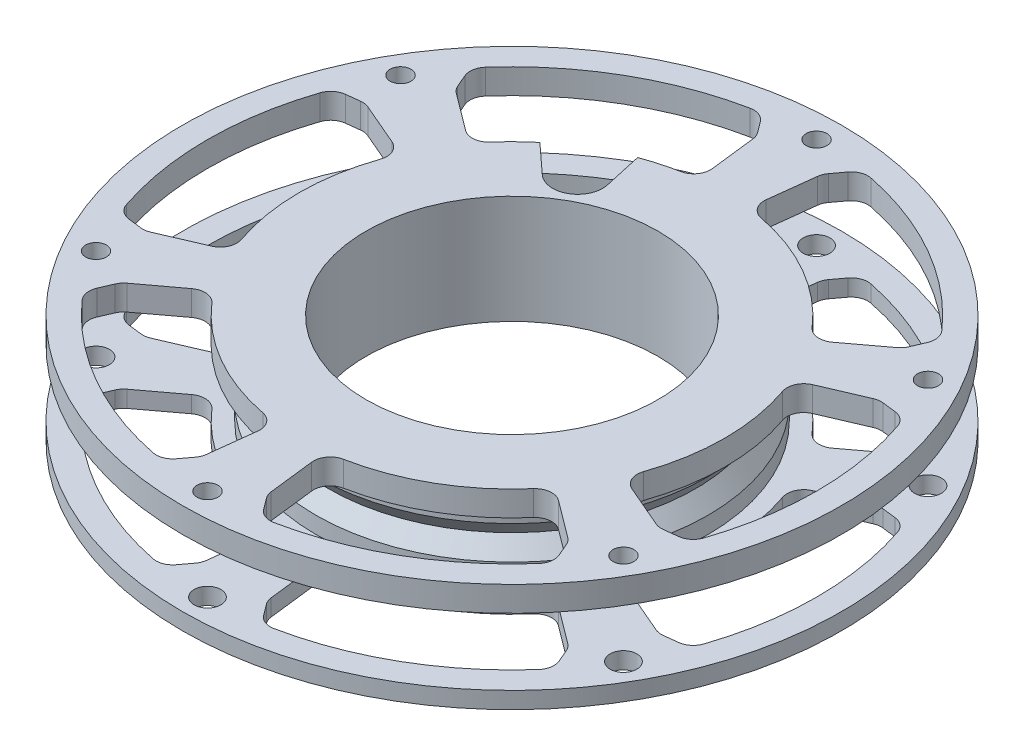
SolidWorks part; units mm, degrees
material "6061 Alloy"
ref_plane "Front Plane" through (0, 0, 0) normal (0, 0, 1) x (1, 0, 0)
ref_plane "Top Plane" through (0, 0, 0) normal (0, 1, 0) x (1, 0, 0)
ref_plane "Right Plane" through (0, 0, 0) normal (1, 0, 0) x (0, 0, -1)
sketch "Sketch1" plane through (0, 0, 0) normal (0, 1, 0) x (1, 0, 0)
  line L0 (0, 0) -> (0, 36.5) construction
  line L1 (0, 0) -> (31.6099, 18.25) construction
  line L2 (0, 0) -> (31.6099, -18.25) construction
  line L3 (0, 0) -> (0, -36.5) construction
  line L4 (0, 0) -> (-31.6099, -18.25) construction
  line L5 (0, 0) -> (-31.6099, 18.25) construction
  point P0 (0, 0)
  point P1 (0, 36.5)
  point P7 (31.6099, 18.25)
  point P9 (31.6099, -18.25)
  point P11 (0, -36.5)
  point P13 (-31.6099, -18.25)
  point P15 (-31.6099, 18.25)
  point P17 (0, 0)
  dimension "D1" = 36.5
  dimension "D2" = 6
sketch "Sketch2" plane through (0, 0, 0) normal (0, 1, 0) x (1, 0, 0)
  line L0 (0, 39.5) -> (12.1614, 39.5) construction
  circle A0 centre (0, 0) radius 39.5
  dimension "D1" = 3
extrude "Boss-Extrude1" add sketch "Sketch2" along normal blind 2
sketch "Sketch5" plane through (0, 2, 0) normal (0, 1, 0) x (1, 0, 0)
  circle A0 centre (0, 0) radius 17.5
  dimension "D1" = 35
extrude "Cut-Extrude1" cut sketch "Sketch5" against normal blind 2
ref_axis "Axis1" through (0, 0, 0) along (0, 1, 0)
sketch "Sketch7" plane through (0, 0, 0) normal (1, 0, 0) x (0, 0, -1)
  line L0 (17.5, 2) -> (17.5, 10)
  line L1 (25, 2) -> (22, 6) construction
  line L2 (17.5, 10) -> (23.5, 10)
  line L7 (17.5, 2) -> (-17.5, 2) construction
  line L8 (23.5, 2) -> (17.5, 2)
  line L9 (17.5, 6) -> (30.0986, 6) construction
  line L10 (22, 6) -> (25, 10) construction
  line L11 (17.5, 10) -> (25, 10) construction
  line L12 (17.5, 2) -> (25, 2) construction
  line L13 (23.5, 8) -> (23.5, 10)
  line L14 (23.5, 4) -> (23.5, 2)
  line L15 (23.5, 8) -> (22, 6)
  line L16 (22, 6) -> (23.5, 4)
  circle A0 centre (22.4938, 6) radius 0.395 construction
  point P8 (0, 0)
  point P15 (0, 0)
  dimension "D1" = 0.79
  dimension "D2" = 3
  dimension "D3" = 6
  dimension "D4" = 8
revolve "Revolve1" add sketch "Sketch7" angle 360 about axis through (0, 0, 0) along (0, 1, 0)
ref_plane "Plane1" through (0, 6, 0) normal (0, 1, 0) x (1, 0, 0)
mirror "Mirror3" about plane through (0, 6, 0) normal (0, 1, 0) of "Cut-Extrude1", "Boss-Extrude1"
sketch "Sketch18" plane through (0, 12, 0) normal (0, 1, 0) x (1, 0, 0)
  circle A0 centre (0, 0) radius 39.5 construction
  circle A1 centre (0, 0) radius 39.5
  circle A2 centre (0, 0) radius 17.5 construction
  circle A3 centre (0, 0) radius 17.5
extrude "Boss-Extrude2" add sketch "Sketch18" along normal blind 1
sketch "Sketch9" plane through (0, 2, 0) normal (0, 1, 0) x (1, 0, 0)
  line L0 (0, 0) -> (-42.0458, 0) construction
  line L1 (-23.4303, -10.0634) -> (-30.781, -13.2205)
  line L2 (-30.781, -13.2205) -> (-34.1751, -12.8184)
  line L3 (-23.4303, 10.0634) -> (-30.781, 13.2205)
  line L4 (-23.4303, -10.0634) -> (-26.0945, -3.8604) construction
  line L5 (0, 0) -> (-31.6099, -18.25) construction
  line L6 (-30.781, 13.2205) -> (-34.1751, 12.8184)
  arc A0 (-23.4303, -10.0634) -> (-23.4303, 10.0634) centre (0, 0) cw
  circle A2 centre (0, 0) radius 25.5
  circle A3 centre (0, 0) radius 25.5 construction
  arc A4 (-34.1751, -12.8184) -> (-34.1751, 12.8184) centre (0, 0) cw
  circle A5 centre (0, 0) radius 36.5
  circle A6 centre (0, 0) radius 36.5 construction
  circle A8 centre (0, 0) radius 33.5
  circle A9 centre (0, 0) radius 33.5 construction
  point P13 (0, 0)
  point P16 (0, 0)
  dimension "D5" = 6
  dimension "D3" = 3
  dimension "D4" = 150
  dimension "D1" = 2
  dimension "D2" = 3
extrude "Cut-Extrude2" cut sketch "Sketch9" against normal through all both and the other way through all
fillet "Fillet1" radius 2 12 edges at (-23.4303, 1, -10.0634) (-30.781, 1, -13.2205) (-34.1751, 1, -12.8184) (-34.1751, 1, 12.8184) (-30.781, 1, 13.2205) (-23.4303, 1, 10.0634) (-34.1751, 11.5, -12.8184) (-30.781, 11.5, -13.2205) (-23.4303, 11.5, -10.0634) (-23.4303, 11.5, 10.0634) (-30.781, 11.5, 13.2205) (-34.1751, 11.5, 12.8184)
pattern_circular "CirPattern1" count 6 over 360 about axis through (0, 0, 0) along (0, 1, 0) of "Cut-Extrude2", "Fillet1"
hole_wizard "M3 Clearance Hole1" positions "Sketch3" profile "Sketch4" hole size "M3" standard "ANSI Metric"
sketch "Sketch3" plane through (0, 2, 0) normal (0, 1, 0) x (1, 0, 0)
  point P0 (0, 36.5)
  point P3 (-31.6099, 18.25)
  point P6 (-31.6099, -18.25)
  point P9 (0, -36.5)
  point P12 (31.6099, -18.25)
  point P15 (31.6099, 18.25)
sketch "Sketch4" plane through (0, 2, -36.5) normal (1, 0, 0) x (0, 0, 1)
  line L0 (0, 0) -> (0, 2)
  line L1 (0, 2) -> (1.6, 2)
  line L2 (1.6, 2) -> (1.6, 0)
  line L5 (1.6, 0) -> (0, 0)
  line L11 (0, -6.35) -> (0, 107.95) construction
  dimension "Thru Hole Dia." = 3.2
  dimension "Thru Hole Depth" = 2
hole_wizard "M3x0.5 Tapped Hole2" positions "Sketch15" profile "Sketch16" tap size "M3x0.5" standard "ANSI Metric" end condition through all
sketch "Sketch15" plane through (0, 13, 0) normal (0, 1, 0) x (1, 0, 0)
  point P0 (31.6099, -18.25)
  point P3 (0, -36.5)
  point P6 (-31.6099, -18.25)
  point P9 (-31.6099, 18.25)
  point P12 (0, 36.5)
  point P15 (31.6099, 18.25)
sketch "Sketch16" plane through (31.6099, 13, 18.25) normal (1, 0, 0) x (0, 0, 1)
  line L0 (0, 0) -> (0, 13)
  line L1 (0, 13) -> (1.25, 13)
  line L2 (1.25, 13) -> (1.25, 0)
  line L5 (1.25, 0) -> (0, 0)
  line L11 (0, -6.35) -> (0, 107.95) construction
  dimension "Thru Tap Drill Dia." = 2.5
  dimension "Thru Tap Drill Depth" = 13
cosmetic thread "Hole Thread9" parameters "D2"=3
cosmetic thread "Hole Thread10" parameters "D2"=3
cosmetic thread "Hole Thread11" parameters "D2"=3
cosmetic thread "Hole Thread12" parameters "D2"=3
cosmetic thread "Hole Thread13" parameters "D2"=3
cosmetic thread "Hole Thread14" parameters "D2"=3
sketch "Sketch10" plane through (0, 13, 0) normal (0, 1, 0) x (1, 0, 0)
  line L0 (0, 0) -> (-10.75, 18.6195) construction
  line L2 (-15.3333, 18.2828) -> (-14.4517, 18.7918) construction
  line L3 (0, 0) -> (-23.3806, 40.4964) construction
  line L4 (0, 0) -> (0, 36.5) construction
  circle A1 centre (-10.75, 18.6195) radius 3 construction
  circle A2 centre (-10.75, 18.6195) radius 2 construction
  circle A3 centre (-10.75, 18.6195) radius 1.5 construction
  circle A4 centre (0, 0) radius 23.5 construction
  point P3 (0, 0)
  point P4 (-4.8634, 21.6032)
  point P12 (0, 0)
  point P16 (-4.8366, 23.3965)
  dimension "D2" = 6
  dimension "D3" = 4
  dimension "D4" = 3
  dimension "D1" = 2
  dimension "D5" = 30
sketch "Sketch11" plane through (0, 13, 0) normal (0, 1, 0) x (1, 0, 0)
  line L0 (-12.7784, 16.4092) -> (-5.75, 9.9593) construction
  line L2 (-5.75, 9.9593) -> (-7.8216, 19.271) construction
  line L3 (-12.7784, 16.4092) -> (-14.794, 18.2589) construction
  line L4 (-7.8216, 19.271) -> (-8.4157, 21.9414) construction
  line L5 (-12.7784, 16.4092) -> (-14.794, 18.2589)
  line L6 (-7.8216, 19.271) -> (-8.4157, 21.9414)
  line L7 (0, 0) -> (-10.75, 18.6195) construction
  line L8 (-8.4157, 21.9414) -> (-9.4719, 26.6892)
  line L9 (-9.4719, 26.6892) -> (-18.2434, 21.4244)
  line L10 (-14.794, 18.2589) -> (-18.2434, 21.4244)
  circle A0 centre (-10.75, 18.6195) radius 3 construction
  circle A1 centre (-10.75, 18.6195) radius 3 construction
  circle A3 centre (0, 0) radius 23.5 construction
  circle A5 centre (0, 0) radius 23.5 construction
  arc A6 (-12.7784, 16.4092) -> (-7.8216, 19.271) centre (-10.75, 18.6195) ccw
  circle A8 centre (0, 0) radius 23.5 construction
  point P5 (0, 0)
  dimension "D1" = 10
extrude "Cut-Extrude3" cut sketch "Sketch11" against normal blind 7.2 contours L6 A6 L5
hole_wizard "M3x0.5 Tapped Hole1" positions "Sketch13" profile "Sketch14" tap size "M3x0.5" standard "ANSI Metric" end condition through all
sketch "Sketch13" plane through (0, 5.8, 0) normal (0, 1, 0) x (1, 0, 0)
  point P4 (-10.75, 18.6195)
  point P14 (0, 0)
sketch "Sketch14" plane through (-10.75, 5.8, -18.6195) normal (1, 0, 0) x (0, 0, 1)
  line L0 (0, 0) -> (0, 5.8)
  line L1 (0, 5.8) -> (1.25, 5.8)
  line L2 (1.25, 5.8) -> (1.25, 0)
  line L5 (1.25, 0) -> (0, 0)
  line L11 (0, -6.35) -> (0, 107.95) construction
  dimension "Thru Tap Drill Dia." = 2.5
  dimension "Thru Tap Drill Depth" = 5.8
cosmetic thread "Hole Thread8" parameters "D2"=3
fillet "Fillet2" radius 0.5 2 edges
